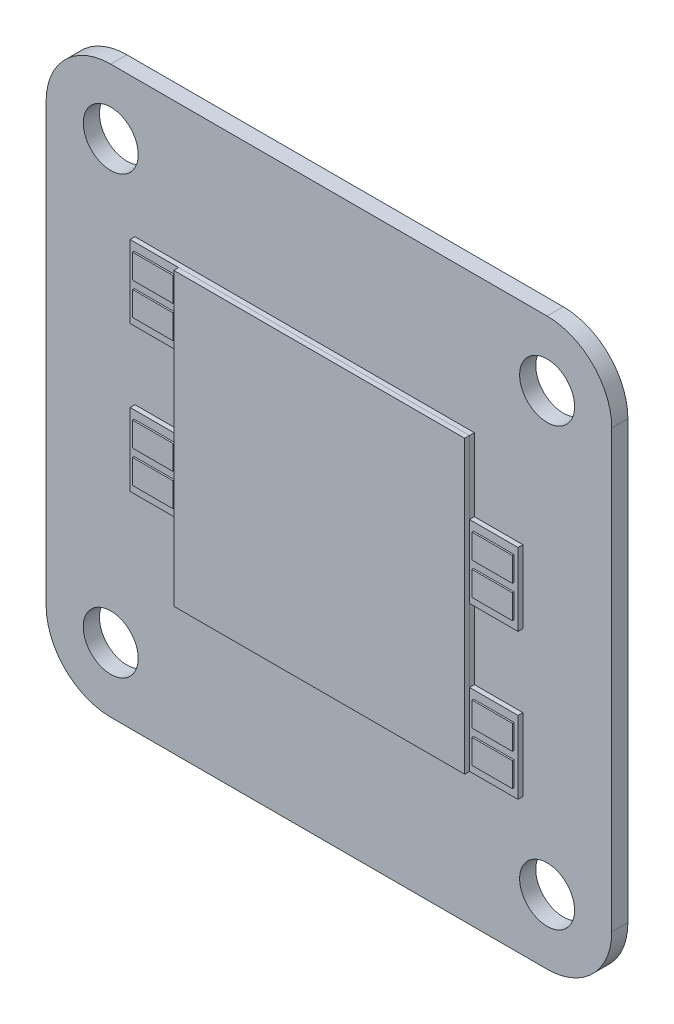
SolidWorks part; units mm, degrees
ref_plane "Ebene vorne" through (0, 0, 0) normal (0, 0, 1) x (1, 0, 0)
ref_plane "Ebene oben" through (0, 0, 0) normal (0, 1, 0) x (1, 0, 0)
ref_plane "Ebene rechts" through (0, 0, 0) normal (1, 0, 0) x (0, 0, -1)
sketch "20" plane through (0, 0, 0) normal (0, 0, 1) x (1, 0, 0)
  line L0 (4, 0) -> (31, 0)
  line L1 (35, 4) -> (35, 31)
  line L2 (31, 35) -> (4, 35)
  line L3 (0, 31) -> (0, 4)
  arc A0 (31, 0) -> (35, 4) centre (31, 4) ccw
  arc A1 (35, 31) -> (31, 35) centre (31, 31) ccw
  arc A2 (4, 35) -> (0, 31) centre (4, 31) ccw
  arc A3 (0, 4) -> (4, 0) centre (4, 4) ccw
  circle A4 centre (4, 4) radius 1.7
  circle A5 centre (31, 4) radius 1.7
  circle A6 centre (31, 31) radius 1.7
  circle A7 centre (4, 31) radius 1.7
sketch "23" plane through (0, 0, 0) normal (0, 0, 1) x (1, 0, 0)
  point P0 (17.5, 17.5)
extrude "Boss-Extrude1" add sketch "20" along normal blind 1
sketch "29" plane through (0, 0, 1) normal (0, 0, 1) x (1, 0, 0)
  line L176 (8.5, 8.5) -> (8.5, 13)
  line L177 (8.5, 13) -> (5.5, 13)
  line L178 (5.5, 13) -> (5.5, 17.5)
  line L179 (5.5, 17.5) -> (8.5, 17.5)
  line L180 (8.5, 17.5) -> (8.5, 22)
  line L181 (8.5, 22) -> (5.5, 22)
  line L182 (5.5, 22) -> (5.5, 26.5)
  line L183 (5.5, 26.5) -> (26.5, 26.5)
  line L184 (26.5, 26.5) -> (26.5, 22)
  line L185 (26.5, 22) -> (29.5, 22)
  line L186 (29.5, 22) -> (29.5, 17.5)
  line L187 (29.5, 17.5) -> (26.5, 17.5)
  line L188 (26.5, 17.5) -> (26.5, 13)
  line L189 (26.5, 13) -> (29.5, 13)
  line L190 (29.5, 13) -> (29.5, 8.5)
  line L191 (29.5, 8.5) -> (8.5, 8.5)
  line L192 (8.5, 8.5) -> (29.5, 8.5)
extrude "Boss-Extrude2" add sketch "29" along normal blind 0.3 contours L191 L190 L189 L188 L187 L186 L185 L184 L183 L182 L181 L180 L179 L178 L177 L176
sketch "Sketch1" plane through (0, 0, 1.3) normal (0, 0, 1) x (1, 0, 0)
  line L0 (29.5, 8.5) -> (8.5, 8.5) construction
  line L1 (8.5, 26.5) -> (26.5, 26.5)
  line L2 (8.5, 26.5) -> (8.5, 8.5)
  line L3 (8.5, 8.5) -> (26.5, 8.5)
  line L4 (26.5, 26.5) -> (26.5, 8.5)
  line L5 (8.5, 26.5) -> (26.5, 8.5) construction
  line L6 (8.5, 8.5) -> (26.5, 26.5) construction
  point P0 (17.5, 17.5)
  dimension "D1" = 18
extrude "Boss-Extrude3" add sketch "Sketch1" along normal blind 0.3 separate body
sketch "Sketch2" plane through (0, 0, 1.3) normal (0, 0, 1) x (1, 0, 0)
  line L0 (29.5, 10.75) -> (26.5, 10.75) construction
  line L1 (29.5, 13) -> (29.5, 8.5) construction
  line L2 (26.5, 8.5) -> (26.5, 26.5) construction
  line L3 (26.75, 11) -> (29.25, 12.5) construction
  line L4 (26.75, 9) -> (29.25, 9)
  line L5 (26.75, 9) -> (26.75, 10.5)
  line L6 (26.75, 10.5) -> (29.25, 10.5)
  line L7 (29.25, 9) -> (29.25, 10.5)
  line L8 (26.75, 9) -> (29.25, 10.5) construction
  line L9 (26.75, 10.5) -> (29.25, 9) construction
  line L10 (26.75, 12.5) -> (29.25, 11) construction
  line L11 (29.25, 12.5) -> (29.25, 11)
  line L12 (26.75, 11) -> (29.25, 11)
  line L13 (26.75, 12.5) -> (26.75, 11)
  line L14 (26.75, 12.5) -> (29.25, 12.5)
  line L15 (29.5, 19.75) -> (26.5, 19.75) construction
  line L16 (29.5, 22) -> (29.5, 17.5) construction
  line L17 (26.5, 8.5) -> (26.5, 26.5) construction
  line L18 (29.5, 22) -> (29.5, 17.5) construction
  line L19 (26.75, 18) -> (29.25, 18)
  line L20 (26.75, 18) -> (26.75, 19.5)
  line L21 (26.75, 19.5) -> (29.25, 19.5)
  line L22 (29.25, 18) -> (29.25, 19.5)
  line L23 (26.75, 18) -> (29.25, 19.5) construction
  line L24 (26.75, 19.5) -> (29.25, 18) construction
  line L25 (26.75, 20) -> (29.25, 21.5) construction
  line L26 (26.75, 21.5) -> (29.25, 20) construction
  line L27 (29.25, 21.5) -> (29.25, 20)
  line L28 (26.75, 20) -> (29.25, 20)
  line L29 (26.75, 21.5) -> (26.75, 20)
  line L30 (26.75, 21.5) -> (29.25, 21.5)
  line L31 (5.5, 15.25) -> (8.5, 15.25) construction
  line L32 (5.5, 13) -> (5.5, 17.5) construction
  line L33 (8.5, 26.5) -> (8.5, 8.5) construction
  line L34 (5.5, 24.25) -> (8.5, 24.25) construction
  line L35 (5.5, 22) -> (5.5, 26.5) construction
  line L36 (8.5, 26.5) -> (8.5, 8.5) construction
  line L37 (5.75, 15.5) -> (8.25, 17) construction
  line L38 (5.75, 13.5) -> (8.25, 13.5)
  line L39 (5.75, 13.5) -> (5.75, 15)
  line L40 (5.75, 15) -> (8.25, 15)
  line L41 (8.25, 13.5) -> (8.25, 15)
  line L42 (5.75, 13.5) -> (8.25, 15) construction
  line L43 (5.75, 15) -> (8.25, 13.5) construction
  line L44 (5.75, 22.5) -> (8.25, 22.5)
  line L45 (5.75, 22.5) -> (5.75, 24)
  line L46 (5.75, 24) -> (8.25, 24)
  line L47 (8.25, 22.5) -> (8.25, 24)
  line L48 (5.75, 22.5) -> (8.25, 24) construction
  line L49 (5.75, 24) -> (8.25, 22.5) construction
  line L50 (5.75, 17) -> (8.25, 15.5) construction
  line L51 (8.25, 17) -> (8.25, 15.5)
  line L52 (5.75, 15.5) -> (8.25, 15.5)
  line L53 (5.75, 17) -> (5.75, 15.5)
  line L54 (5.75, 17) -> (8.25, 17)
  line L55 (5.75, 24.5) -> (8.25, 26) construction
  line L56 (5.75, 26) -> (8.25, 24.5) construction
  line L57 (8.25, 26) -> (8.25, 24.5)
  line L58 (5.75, 24.5) -> (8.25, 24.5)
  line L59 (5.75, 26) -> (5.75, 24.5)
  line L60 (5.75, 26) -> (8.25, 26)
  point P6 (28, 9.75)
  point P15 (28, 11.75)
  point P22 (28, 18.75)
  point P34 (28, 20.75)
  point P46 (7, 14.25)
  point P51 (7, 23.25)
  point P60 (7, 16.25)
  point P65 (7, 25.25)
  dimension "D1" = 1
  dimension "D2" = 1.5
  dimension "D3" = 2.5
  dimension "D4" = 1.5
  dimension "D5" = 2.5
  dimension "D6" = 1.5
  dimension "D7" = 1.5
  dimension "D8" = 1
  dimension "D9" = 2.5
  dimension "D10" = 1.5
  dimension "D11" = 1.5
  dimension "D12" = 1
  dimension "D13" = 1
  dimension "D14" = 1.5
extrude "Boss-Extrude4" add sketch "Sketch2" along normal blind 0.1
